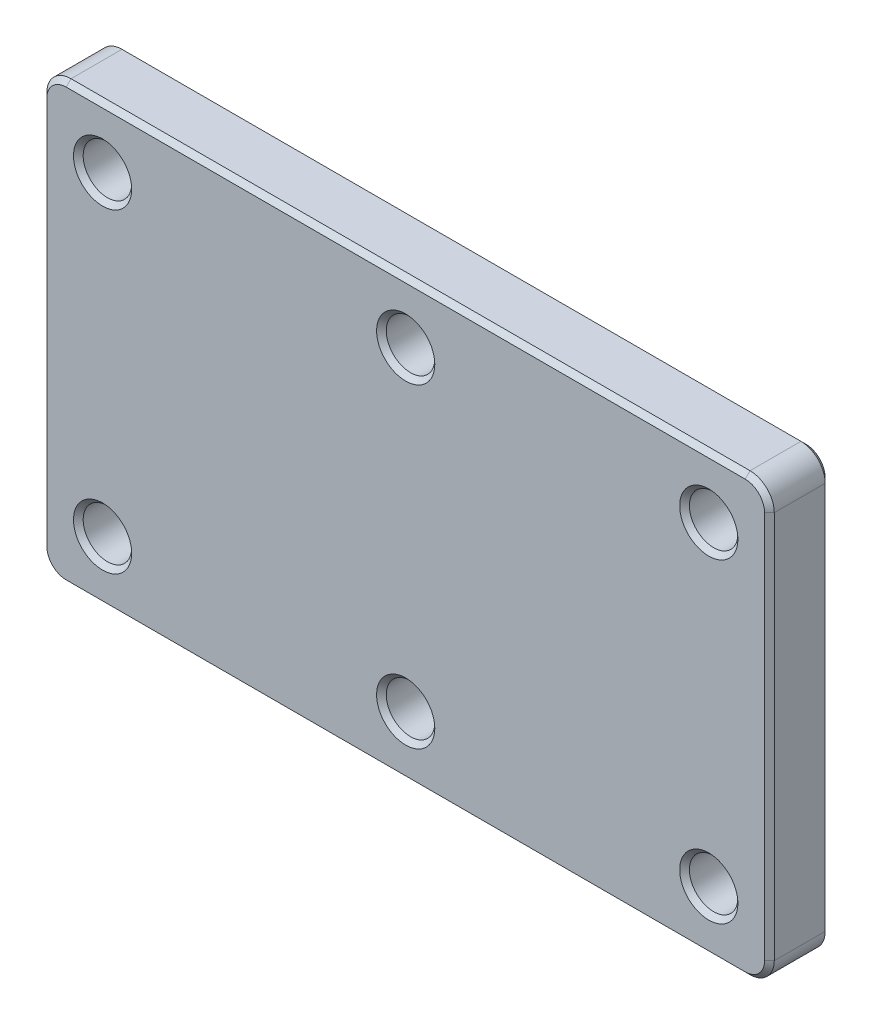
SolidWorks part; units mm, degrees
ref_plane "Front Plane" through (0, 0, 0) normal (0, 0, 1) x (1, 0, 0)
ref_plane "Top Plane" through (0, 0, 0) normal (0, 1, 0) x (1, 0, 0)
ref_plane "Right Plane" through (0, 0, 0) normal (1, 0, 0) x (0, 0, -1)
sketch "Sketch1" plane through (0, 0, 0) normal (0, 0, 1) x (1, 0, 0)
  line L0 (-156.5905, 0) -> (172.4077, 0) construction
  line L1 (0, 112.4605) -> (0, -116.2566) construction
  line L2 (-140, 90) -> (140, 90)
  line L3 (150, 80) -> (150, -80)
  line L4 (140, -90) -> (-140, -90)
  line L5 (-150, -80) -> (-150, 80)
  line L6 (-125, 65) -> (0, 65) construction
  circle A0 centre (-125, -65) radius 10
  circle A1 centre (0, -65) radius 10
  circle A2 centre (125, -65) radius 10
  circle A3 centre (125, 65) radius 10
  circle A4 centre (0, 65) radius 10
  circle A5 centre (-125, 65) radius 10
  arc A6 (-150, -80) -> (-140, -90) centre (-140, -80) ccw
  arc A7 (140, -90) -> (150, -80) centre (140, -80) ccw
  arc A8 (150, 80) -> (140, 90) centre (140, 80) ccw
  arc A9 (-150, 80) -> (-140, 90) centre (-140, 80) cw
  point P22 (0, 0)
  point P23 (0, 65)
  dimension "D5" = 20
  dimension "D6" = 10
  dimension "D1" = 180
  dimension "D2" = 300
  dimension "D3" = 130
  dimension "D4" = 250
extrude "Boss-Extrude1" add sketch "Sketch1" against normal blind 25
chamfer "Chamfer1" distance 2 angle 45 28 edges at (-135, 65, -25) (-10, 65, -25) (115, 65, -25) (135, -65, -25) (10, -65, -25) (-115, -65, -25) (147.0711, -87.0711, -25) (0, -90, -25) (-147.0711, -87.0711, -25) (-150, 0, -25) (-147.0711, 87.0711, -25) (0, 90, -25) (147.0711, 87.0711, -25) (150, 0, -25) (147.0711, 87.0711, 0) (150, 0, 0) (147.0711, -87.0711, 0) (0, 90, 0) (-147.0711, 87.0711, 0) (-150, 0, 0) (-147.0711, -87.0711, 0) (0, -90, 0) (-115, -65, 0) (10, -65, 0) (135, -65, 0) (115, 65, 0) (-10, 65, 0) (-135, 65, 0)
